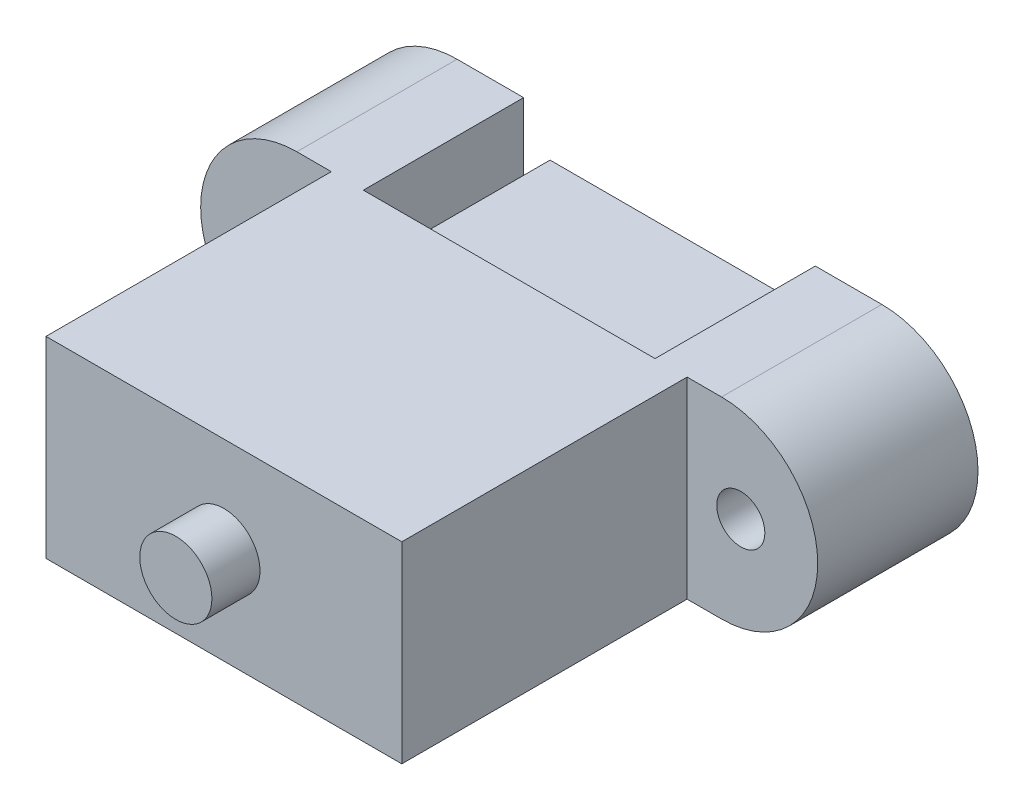
SolidWorks part; units mm, degrees
ref_plane "Alzado" through (0, 0, 0) normal (0, 0, 1) x (1, 0, 0)
ref_plane "Planta" through (0, 0, 0) normal (0, 1, 0) x (1, 0, 0)
ref_plane "Vista lateral" through (0, 0, 0) normal (1, 0, 0) x (0, 0, -1)
sketch "Croquis1" plane through (0, 0, 0) normal (0, 0, 1) x (1, 0, 0)
  line L0 (-19.25, 0) -> (19.25, 0) construction
  line L1 (19.25, -6) -> (-19.25, -6) construction
  line L2 (19.25, 6) -> (19.25, -6) construction
  line L3 (19.25, 6) -> (-19.25, 6) construction
  line L4 (-19.25, -6) -> (-19.25, 6) construction
  line L5 (19.25, -6) -> (-19.25, 6) construction
  line L6 (19.25, 6) -> (-19.25, -6) construction
  line L7 (-9.1, 6) -> (-9.1, -6)
  line L8 (-9.1, -6) -> (0, 0) construction
  line L9 (0, 0) -> (9.1, 6) construction
  line L10 (9.1, 6) -> (9.1, -6)
  line L11 (-13.25, 6) -> (-9.1, 6)
  line L12 (-13.25, -6) -> (-9.1, -6)
  line L13 (9.1, -6) -> (13.25, -6)
  line L14 (9.1, 6) -> (13.25, 6)
  line L15 (-14.45, 0) -> (-14.45, -9.5275) construction
  line L16 (-14.45, -9.5275) -> (-9.1, -6) construction
  line L17 (9.1, 6) -> (14.45, 9.5275) construction
  line L18 (14.45, 9.5275) -> (14.45, 0) construction
  arc A0 (-13.25, -6) -> (-13.25, 6) centre (-13.25, 0) cw
  arc A1 (13.25, 6) -> (13.25, -6) centre (13.25, 0) cw
  circle A2 centre (-14.45, 0) radius 2.55 construction
  circle A3 centre (14.45, 0) radius 2.55 construction
  circle A4 centre (-14.45, 0) radius 1.5
  circle A5 centre (14.45, 0) radius 1.5
  point P0 (0, 0)
  point P23 (-17, 0)
  point P24 (17, 0)
  dimension "D4" = 5.1
  dimension "D6" = 3
  dimension "D1" = 38.5
  dimension "D2" = 12
  dimension "D3" = 18.2
  dimension "D5" = 34
extrude "Saliente-Extruir1" add sketch "Croquis1" along normal blind 10
sketch "Croquis2" plane through (0, 0, 10) normal (0, 0, 1) x (1, 0, 0)
  line L0 (-9.1, 6) -> (-13.25, 6) construction
  line L1 (11.1, -6) -> (-11.1, -6)
  line L2 (11.1, -6) -> (11.1, 6)
  line L3 (11.1, 6) -> (-11.1, 6)
  line L4 (-11.1, -6) -> (-11.1, 6)
  line L5 (11.1, -6) -> (-11.1, 6) construction
  line L6 (11.1, 6) -> (-11.1, -6) construction
  line L7 (-9.1, -6) -> (-9.1, 6) construction
  point P0 (0, 0)
  dimension "D1" = 2
extrude "Saliente-Extruir2" add sketch "Croquis2" along normal blind 17.8
sketch "Croquis3" plane through (0, 0, 27.8) normal (0, 0, 1) x (1, 0, 0)
  circle A0 centre (0, 0) radius 2.25
  dimension "D1" = 4.5
extrude "Saliente-Extruir3" add sketch "Croquis3" along normal blind 3
sketch "Croquis4" plane through (0, 0, 10) normal (0, 0, -1) x (-1, 0, 0)
  line L1 (7.45, 3.45) -> (-7.45, 3.45)
  line L2 (7.45, 3.45) -> (7.45, -3.45)
  line L3 (7.45, -3.45) -> (-7.45, -3.45)
  line L4 (-7.45, 3.45) -> (-7.45, -3.45)
  line L5 (7.45, 3.45) -> (-7.45, -3.45) construction
  line L6 (7.45, -3.45) -> (-7.45, 3.45) construction
  point P0 (0, 0)
  dimension "D1" = 6.9
  dimension "D2" = 14.9
extrude "Saliente-Extruir4" add sketch "Croquis4" along normal up to surface (10 mm away) up to face at (12.675, 0, 0)
sketch "Croquis5" plane through (0, 0, 0) normal (0, 0, -1) x (-1, 0, 0)
  line L0 (0, 0.915) -> (0, 0) construction
  line L1 (5.4, 1.83) -> (-5.4, 1.83)
  line L2 (5.4, 1.83) -> (5.4, 0)
  line L3 (5.4, 0) -> (-5.4, 0)
  line L4 (-5.4, 1.83) -> (-5.4, 0)
  line L5 (5.4, 1.83) -> (-5.4, 0) construction
  line L6 (5.4, 0) -> (-5.4, 1.83) construction
  line L7 (-7.45, 3.45) -> (-7.45, -3.45) construction
  line L8 (6.45, -2.45) -> (-6.45, -2.45)
  line L9 (6.45, -2.45) -> (6.45, 2.45)
  line L10 (6.45, 2.45) -> (-6.45, 2.45)
  line L11 (-6.45, -2.45) -> (-6.45, 2.45)
  line L12 (6.45, -2.45) -> (-6.45, 2.45) construction
  line L13 (6.45, 2.45) -> (-6.45, -2.45) construction
  line L14 (-7.45, -3.45) -> (7.45, -3.45) construction
  point P0 (0, 0.915)
  dimension "D1" = 1.83
  dimension "D2" = 10.8
  dimension "D3" = 1
  dimension "D4" = 1
extrude "Cortar-Extruir1" cut sketch "Croquis5" against normal blind 10.5
